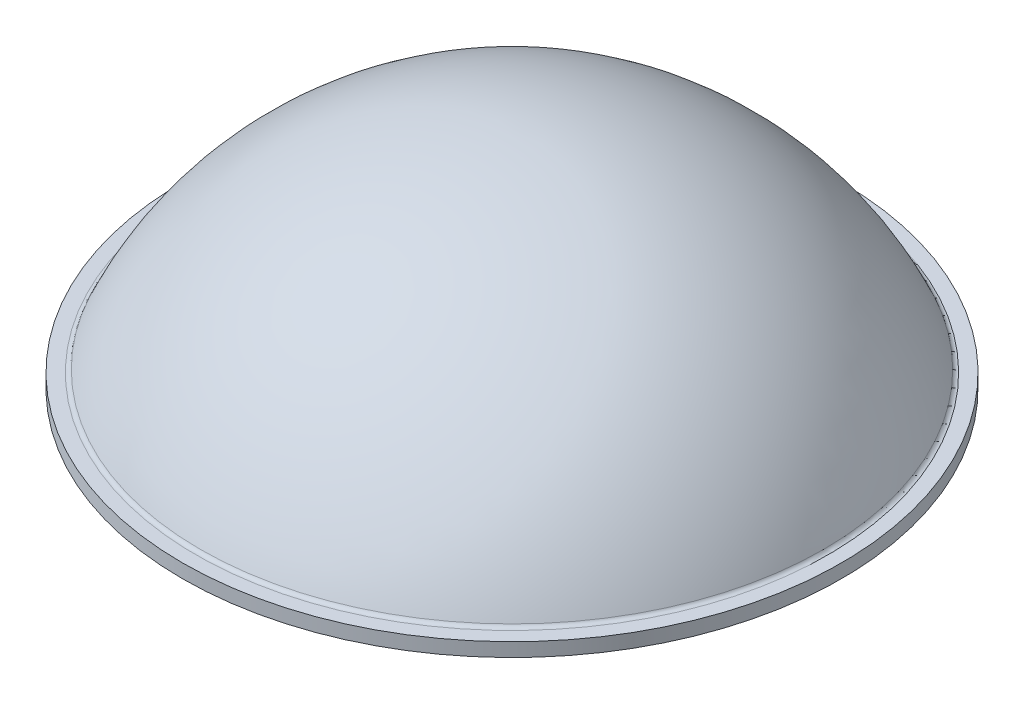
SolidWorks part; units mm, degrees
ref_plane "Front" through (0, 0, 0) normal (0, 0, 1) x (1, 0, 0)
ref_plane "Top" through (0, 0, 0) normal (0, 1, 0) x (1, 0, 0)
ref_plane "Right" through (0, 0, 0) normal (1, 0, 0) x (0, 0, -1)
sketch "Sketch1" plane through (0, 0, 0) normal (1, 0, 0) x (0, 0, -1)
  line L0 (0, 0) -> (0, 3.175) construction
  line L1 (-4.7625, 0) -> (4.7625, 0) construction
  line L2 (0, 3.175) -> (-4.7625, 3.175) construction
  line L3 (-4.7625, 3.175) -> (-4.7625, 0) construction
  dimension "Height" = 3.175
  dimension "OD" = 9.525
sketch "Sketch2" plane through (0, 0, 0) normal (1, 0, 0) x (0, 0, -1)
  line L0 (-4.7625, 0) -> (-4.7625, 0.1984)
  line L1 (-4.7625, 0.1984) -> (-4.5641, 0.1984)
  line L2 (0, 3.175) -> (0, 0)
  line L3 (0, 0) -> (-4.7625, 0)
  line L4 (0, 3.175) -> (-4.7625, 3.175) construction
  arc A0 (-4.5035, 0.2379) -> (0, 3.175) centre (0, -1.7463) cw
  arc A1 (-4.5035, 0.2379) -> (-4.5641, 0.1984) centre (-4.5641, 0.2646) cw
  dimension "D2" = 0.0661
  dimension "D1" = 0.1984
revolve "Revolve1" add sketch "Sketch2" angle 360 about L0
sketch "Sketch3" plane through (0, 0, 0) normal (0, 0, 1) x (1, 0, 0)
  line L0 (0, 3.175) -> (-4.7625, 3.175) construction
  line L1 (0, 3.175) -> (0, 0) construction
  line L2 (-4.7625, 3.175) -> (-4.7625, 0) construction
  line L3 (-4.7625, 0) -> (0, 0) construction
  line L4 (-4.7625, 0) -> (4.7625, 0) construction
  line L5 (-4.7625, 0) -> (-4.7845, 0) construction
  dimension "D1" = 0.022
equation "\"D1@Sketch2\"=\"Height@Sketch1\"/16"
equation "\"D2@Sketch2\"=\"D1@Sketch2\"/3"
equation "\"D1@Sketch3\"=\"D2@Sketch2\"/3"
